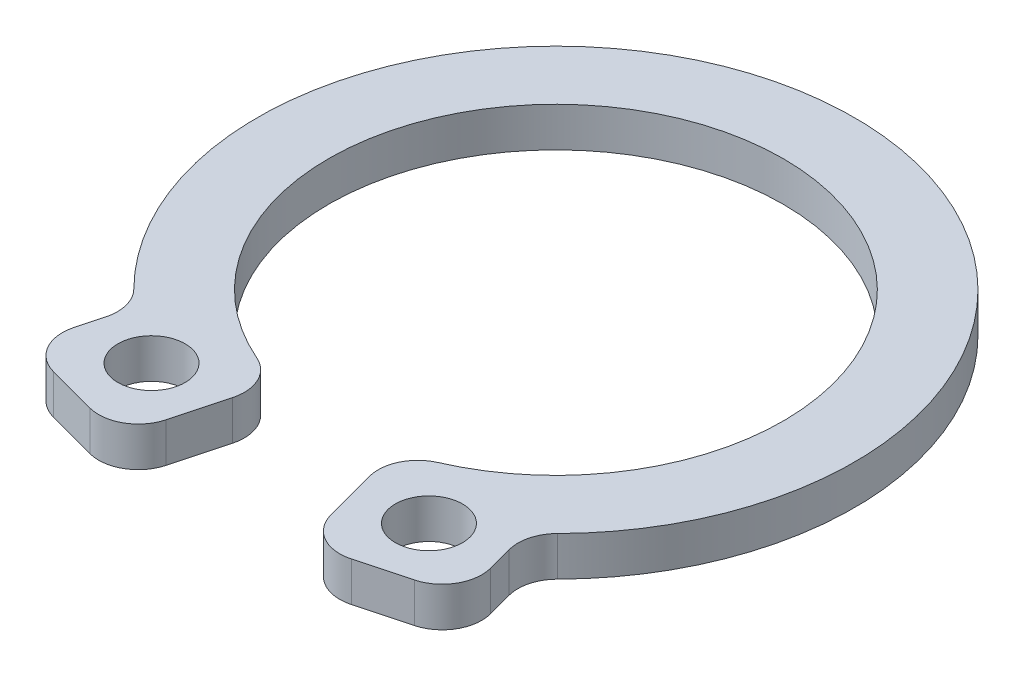
SolidWorks part; units mm, degrees
ref_plane "Front Plane" through (0, 0, 0) normal (0, 0, 1) x (1, 0, 0)
ref_plane "Top Plane" through (0, 0, 0) normal (0, 1, 0) x (1, 0, 0)
ref_plane "Right Plane" through (0, 0, 0) normal (1, 0, 0) x (0, 0, -1)
sketch "Sketch1" plane through (0, 0, 0) normal (0, 1, 0) x (1, 0, 0)
  line L0 (0, 0) -> (0, -7.55) construction
  line L1 (0, 0) -> (-2.3423, -8.7416)
  line L4 (0, 0) -> (2.3423, -8.7416)
  line L5 (-1.4882, -5.5541) -> (-0.3758, -5.8521) construction
  line L6 (-0.3758, -5.8521) -> (-1.2299, -9.0397) construction
  line L7 (-1.2299, -9.0397) -> (-2.3423, -8.7416) construction
  line L8 (-2.3423, -8.7416) -> (-5.5299, -7.8875)
  line L9 (-3.509, -6.7208) -> (-0.8029, -7.4459) construction
  line L10 (-5.5299, -7.8875) -> (-4.9451, -5.7051)
  line L11 (-3.509, -6.7208) -> (-3.9361, -8.3146) construction
  line L12 (3.509, -6.7208) -> (3.9361, -8.3146) construction
  line L13 (3.509, -6.7208) -> (0.8029, -7.4459) construction
  line L14 (1.2299, -9.0397) -> (2.3423, -8.7416) construction
  line L15 (0.3758, -5.8521) -> (1.2299, -9.0397) construction
  line L16 (1.4882, -5.5541) -> (0.3758, -5.8521) construction
  line L17 (5.5299, -7.8875) -> (4.9451, -5.7051)
  line L18 (2.3423, -8.7416) -> (5.5299, -7.8875)
  arc A0 (1.4882, -5.5541) -> (-1.4882, -5.5541) centre (0, 0) ccw
  arc A1 (4.9451, -5.7051) -> (-4.9451, -5.7051) centre (0, 0) ccw
  circle A2 centre (-3.509, -6.7208) radius 0.85
  circle A3 centre (3.509, -6.7208) radius 0.85
  dimension "D1" = 11.5
  dimension "D2" = 1.8
  dimension "D4" = 9.05
  dimension "D5" = 1.7
  dimension "D3" = 15
  dimension "D6" = 3.3
extrude "Boss-Extrude1" add sketch "Sketch1" along normal blind 1 contours L17 A1 L10 L8 L1 A0 L4 L18 A2 A3
fillet "Fillet1" radius 1 8 edges at (-4.9451, 0.5, 5.7051) (5.5299, 0.5, 7.8875) (4.9451, 0.5, 5.7051) (1.4882, 0.5, 5.5541) (2.3423, 0.5, 8.7416) (-1.4882, 0.5, 5.5541) (-5.5299, 0.5, 7.8875) (-2.3423, 0.5, 8.7416)
